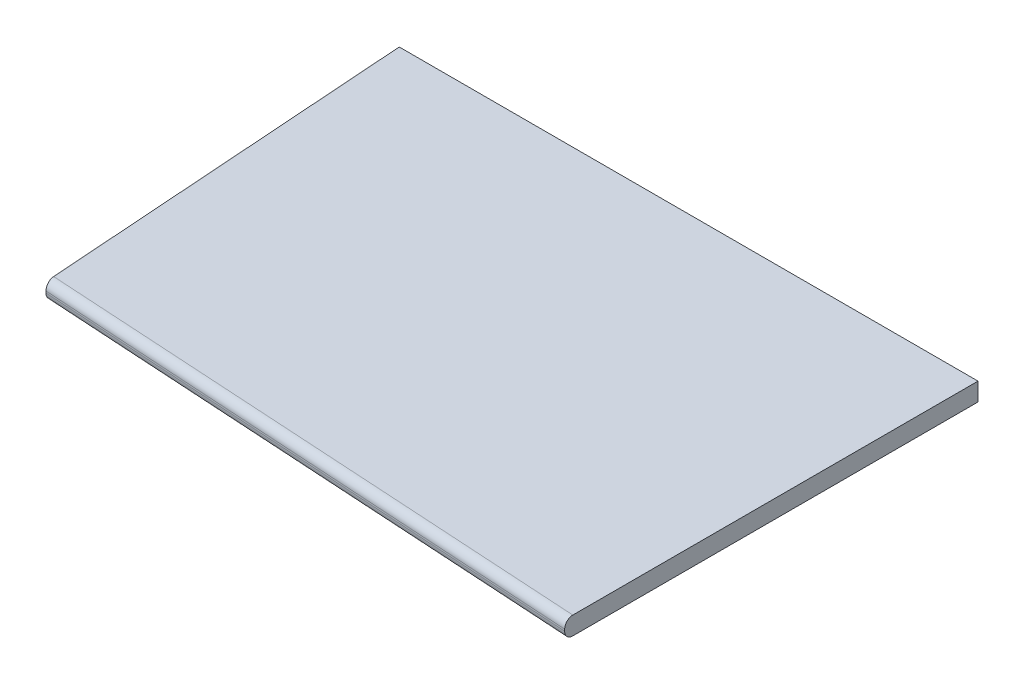
SolidWorks part; units mm, degrees
material "PS HI"
ref_plane "Front Plane" through (0, 0, 0) normal (0, 0, 1) x (1, 0, 0)
ref_plane "Top Plane" through (0, 0, 0) normal (0, 1, 0) x (1, 0, 0)
ref_plane "Right Plane" through (0, 0, 0) normal (1, 0, 0) x (0, 0, -1)
sketch "Sketch1" plane through (0, 0, 0) normal (0, 1, 0) x (1, 0, 0)
  line L0 (0, 0) -> (81.28, 0)
  line L1 (81.28, 0) -> (81.28, -58.049)
  line L2 (81.28, -58.049) -> (3.7299, -53.34)
  line L3 (3.7299, -53.34) -> (0, 0)
  dimension "D1" = 86
  dimension "D2" = 81.28
  dimension "D3" = 53.34
extrude "Boss-Extrude1" add sketch "Sketch1" along normal mid plane 2.54
fillet "Fillet1" radius 1.143 2 edges at (42.5049, -1.27, 55.6945) (42.5049, 1.27, 55.6945)
